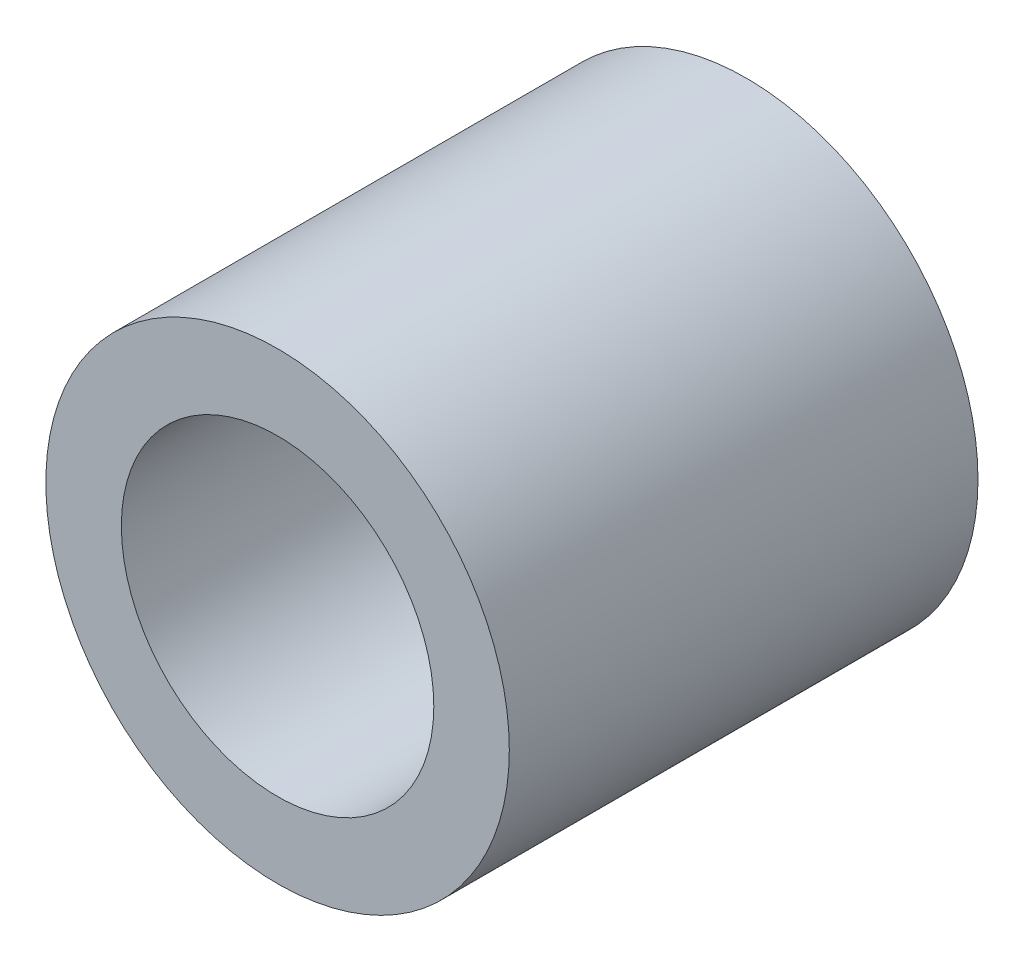
SolidWorks part; units mm, degrees
ref_plane "前基準面" through (0, 0, 0) normal (0, 0, 1) x (1, 0, 0)
ref_plane "上基準面" through (0, 0, 0) normal (0, 1, 0) x (1, 0, 0)
ref_plane "右基準面" through (0, 0, 0) normal (1, 0, 0) x (0, 0, -1)
sketch "草圖1" plane through (0, 0, 0) normal (0, 0, 1) x (1, 0, 0)
  circle A0 centre (0, 0) radius 3
  circle A1 centre (0, 0) radius 4.45
  dimension "D1" = 6
  dimension "D2" = 8.9
extrude "填料-伸長1" add sketch "草圖1" along normal blind 9
